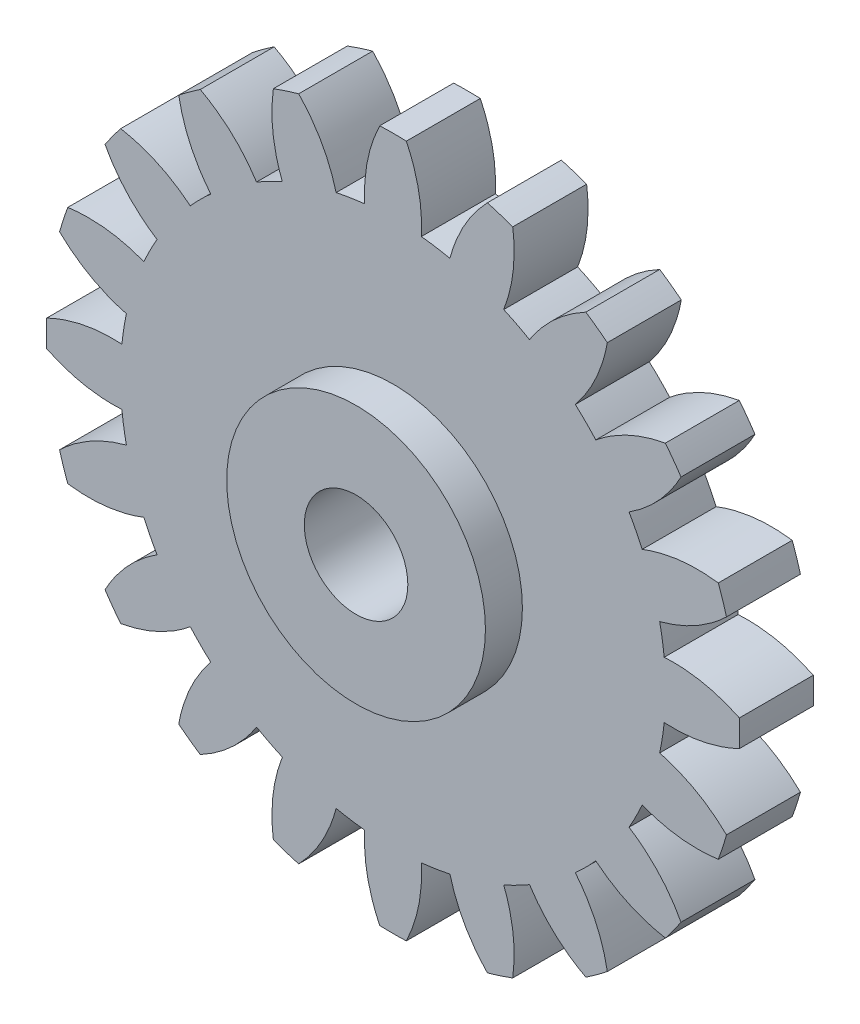
SolidWorks part; units mm, degrees
ref_plane "Front" through (0, 0, 0) normal (0, 0, 1) x (1, 0, 0)
ref_plane "Top" through (0, 0, 0) normal (0, 1, 0) x (1, 0, 0)
ref_plane "Right" through (0, 0, 0) normal (1, 0, 0) x (0, 0, -1)
sketch "草图1" plane through (0, 0, 0) normal (0, 0, 1) x (1, 0, 0)
  line L0 (0, 5.5081) -> (0, -0.6703) construction
  line L1 (0, 0) -> (-0.6106, 5.8096) construction
  line L2 (0, 0) -> (0.5998, 5.7068) construction
  arc A0 (-0.3826, 3.6676) -> (-0.7695, 3.6063) centre (0, 0) ccw
  arc A1 (0.18, 4.684) -> (-0.18, 4.684) centre (0, 0) ccw
  arc A3 (1.6186, 4.3992) -> (1.2763, 4.5104) centre (0, 0) ccw
  arc A4 (2.8988, 3.6837) -> (2.6076, 3.8953) centre (0, 0) ccw
  arc A5 (3.8953, 2.6076) -> (3.6837, 2.8988) centre (0, 0) ccw
  arc A6 (4.5104, 1.2763) -> (4.3992, 1.6186) centre (0, 0) ccw
  arc A7 (4.684, -0.18) -> (4.684, 0.18) centre (0, 0) ccw
  arc A8 (4.3992, -1.6186) -> (4.5104, -1.2763) centre (0, 0) ccw
  arc A9 (3.6837, -2.8988) -> (3.8953, -2.6076) centre (0, 0) ccw
  arc A10 (2.6076, -3.8953) -> (2.8988, -3.6837) centre (0, 0) ccw
  arc A11 (1.2763, -4.5104) -> (1.6186, -4.3992) centre (0, 0) ccw
  arc A12 (-0.18, -4.684) -> (0.18, -4.684) centre (0, 0) ccw
  arc A13 (-1.6186, -4.3992) -> (-1.2763, -4.5104) centre (0, 0) ccw
  arc A14 (-2.8988, -3.6837) -> (-2.6076, -3.8953) centre (0, 0) ccw
  arc A15 (-3.8953, -2.6076) -> (-3.6837, -2.8988) centre (0, 0) ccw
  arc A16 (-4.5104, -1.2763) -> (-4.3992, -1.6186) centre (0, 0) ccw
  arc A17 (-4.684, 0.18) -> (-4.684, -0.18) centre (0, 0) ccw
  arc A18 (-4.3992, 1.6186) -> (-4.5104, 1.2763) centre (0, 0) ccw
  arc A19 (-3.6837, 2.8988) -> (-3.8953, 2.6076) centre (0, 0) ccw
  arc A20 (-2.6076, 3.8953) -> (-2.8988, 3.6837) centre (0, 0) ccw
  arc A21 (-1.2763, 4.5104) -> (-1.6186, 4.3992) centre (0, 0) ccw
  arc A22 (0.7695, 3.6063) -> (0.3826, 3.6676) centre (0, 0) ccw
  arc A23 (1.8462, 3.192) -> (1.4972, 3.3699) centre (0, 0) ccw
  arc A24 (2.7422, 2.4653) -> (2.4653, 2.7422) centre (0, 0) ccw
  arc A25 (3.3699, 1.4972) -> (3.192, 1.8462) centre (0, 0) ccw
  arc A26 (3.6676, 0.3826) -> (3.6063, 0.7695) centre (0, 0) ccw
  arc A27 (3.6063, -0.7695) -> (3.6676, -0.3826) centre (0, 0) ccw
  arc A28 (3.192, -1.8462) -> (3.3699, -1.4972) centre (0, 0) ccw
  arc A29 (2.4653, -2.7422) -> (2.7422, -2.4653) centre (0, 0) ccw
  arc A30 (1.4972, -3.3699) -> (1.8462, -3.192) centre (0, 0) ccw
  arc A31 (-1.4972, 3.3699) -> (-1.8462, 3.192) centre (0, 0) ccw
  arc A32 (-2.4653, 2.7422) -> (-2.7422, 2.4653) centre (0, 0) ccw
  arc A33 (-3.192, 1.8462) -> (-3.3699, 1.4972) centre (0, 0) ccw
  arc A34 (-3.6063, 0.7695) -> (-3.6676, 0.3826) centre (0, 0) ccw
  arc A35 (-3.6676, -0.3826) -> (-3.6063, -0.7695) centre (0, 0) ccw
  arc A36 (-3.3699, -1.4972) -> (-3.192, -1.8462) centre (0, 0) ccw
  arc A37 (-2.7422, -2.4653) -> (-2.4653, -2.7422) centre (0, 0) ccw
  arc A38 (-1.8462, -3.192) -> (-1.4972, -3.3699) centre (0, 0) ccw
  arc A39 (-0.7695, -3.6063) -> (-0.3826, -3.6676) centre (0, 0) ccw
  arc A40 (0.3826, -3.6676) -> (0.7695, -3.6063) centre (0, 0) ccw
  spline S0 degree 2 poles (0.18, 4.684) (0.4125, 4.2014) (0.3826, 3.6676) knots 0 0 0 1 1 1
  spline S1 degree 2 poles (-0.18, 4.684) (-0.4125, 4.2014) (-0.3826, 3.6676) knots 0 0 0 1 1 1
  spline S2 degree 2 poles (1.2763, 4.5104) (0.906, 4.1233) (0.7695, 3.6063) knots 0 0 0 1 1 1
  spline S3 degree 2 poles (1.6186, 4.3992) (1.6907, 3.8683) (1.4972, 3.3699) knots 0 0 0 1 1 1
  spline S4 degree 2 poles (2.6076, 3.8953) (2.1358, 3.6415) (1.8462, 3.192) knots 0 0 0 1 1 1
  spline S5 degree 2 poles (2.8988, 3.6837) (2.8033, 3.1566) (2.4653, 2.7422) knots 0 0 0 1 1 1
  spline S6 degree 2 poles (3.6837, 2.8988) (3.1566, 2.8033) (2.7422, 2.4653) knots 0 0 0 1 1 1
  spline S7 degree 2 poles (3.8953, 2.6076) (3.6415, 2.1358) (3.192, 1.8462) knots 0 0 0 1 1 1
  spline S8 degree 2 poles (4.3992, 1.6186) (3.8683, 1.6907) (3.3699, 1.4972) knots 0 0 0 1 1 1
  spline S9 degree 2 poles (4.5104, 1.2763) (4.1233, 0.906) (3.6063, 0.7695) knots 0 0 0 1 1 1
  spline S10 degree 2 poles (4.684, 0.18) (4.2014, 0.4125) (3.6676, 0.3826) knots 0 0 0 1 1 1
  spline S11 degree 2 poles (4.684, -0.18) (4.2014, -0.4125) (3.6676, -0.3826) knots 0 0 0 1 1 1
  spline S12 degree 2 poles (4.5104, -1.2763) (4.1233, -0.906) (3.6063, -0.7695) knots 0 0 0 1 1 1
  spline S13 degree 2 poles (4.3992, -1.6186) (3.8683, -1.6907) (3.3699, -1.4972) knots 0 0 0 1 1 1
  spline S14 degree 2 poles (3.8953, -2.6076) (3.6415, -2.1358) (3.192, -1.8462) knots 0 0 0 1 1 1
  spline S15 degree 2 poles (3.6837, -2.8988) (3.1566, -2.8033) (2.7422, -2.4653) knots 0 0 0 1 1 1
  spline S16 degree 2 poles (2.8988, -3.6837) (2.8033, -3.1566) (2.4653, -2.7422) knots 0 0 0 1 1 1
  spline S17 degree 2 poles (2.6076, -3.8953) (2.1358, -3.6415) (1.8462, -3.192) knots 0 0 0 1 1 1
  spline S18 degree 2 poles (1.6186, -4.3992) (1.6907, -3.8683) (1.4972, -3.3699) knots 0 0 0 1 1 1
  spline S19 degree 2 poles (1.2763, -4.5104) (0.906, -4.1233) (0.7695, -3.6063) knots 0 0 0 1 1 1
  spline S20 degree 2 poles (0.18, -4.684) (0.4125, -4.2014) (0.3826, -3.6676) knots 0 0 0 1 1 1
  spline S21 degree 2 poles (-0.18, -4.684) (-0.4125, -4.2014) (-0.3826, -3.6676) knots 0 0 0 1 1 1
  spline S22 degree 2 poles (-1.2763, -4.5104) (-0.906, -4.1233) (-0.7695, -3.6063) knots 0 0 0 1 1 1
  spline S23 degree 2 poles (-1.6186, -4.3992) (-1.6907, -3.8683) (-1.4972, -3.3699) knots 0 0 0 1 1 1
  spline S24 degree 2 poles (-2.6076, -3.8953) (-2.1358, -3.6415) (-1.8462, -3.192) knots 0 0 0 1 1 1
  spline S25 degree 2 poles (-2.8988, -3.6837) (-2.8033, -3.1566) (-2.4653, -2.7422) knots 0 0 0 1 1 1
  spline S26 degree 2 poles (-3.6837, -2.8988) (-3.1566, -2.8033) (-2.7422, -2.4653) knots 0 0 0 1 1 1
  spline S27 degree 2 poles (-3.8953, -2.6076) (-3.6415, -2.1358) (-3.192, -1.8462) knots 0 0 0 1 1 1
  spline S28 degree 2 poles (-4.3992, -1.6186) (-3.8683, -1.6907) (-3.3699, -1.4972) knots 0 0 0 1 1 1
  spline S29 degree 2 poles (-4.5104, -1.2763) (-4.1233, -0.906) (-3.6063, -0.7695) knots 0 0 0 1 1 1
  spline S30 degree 2 poles (-4.684, -0.18) (-4.2014, -0.4125) (-3.6676, -0.3826) knots 0 0 0 1 1 1
  spline S31 degree 2 poles (-4.684, 0.18) (-4.2014, 0.4125) (-3.6676, 0.3826) knots 0 0 0 1 1 1
  spline S32 degree 2 poles (-4.5104, 1.2763) (-4.1233, 0.906) (-3.6063, 0.7695) knots 0 0 0 1 1 1
  spline S33 degree 2 poles (-4.3992, 1.6186) (-3.8683, 1.6907) (-3.3699, 1.4972) knots 0 0 0 1 1 1
  spline S34 degree 2 poles (-3.8953, 2.6076) (-3.6415, 2.1358) (-3.192, 1.8462) knots 0 0 0 1 1 1
  spline S35 degree 2 poles (-3.6837, 2.8988) (-3.1566, 2.8033) (-2.7422, 2.4653) knots 0 0 0 1 1 1
  spline S36 degree 2 poles (-2.8988, 3.6837) (-2.8033, 3.1566) (-2.4653, 2.7422) knots 0 0 0 1 1 1
  spline S37 degree 2 poles (-2.6076, 3.8953) (-2.1358, 3.6415) (-1.8462, 3.192) knots 0 0 0 1 1 1
  spline S38 degree 2 poles (-1.6186, 4.3992) (-1.6907, 3.8683) (-1.4972, 3.3699) knots 0 0 0 1 1 1
  spline S39 degree 2 poles (-1.2763, 4.5104) (-0.906, 4.1233) (-0.7695, 3.6063) knots 0 0 0 1 1 1
  point P7 (0, 4.6875)
  point P10 (0, 4.1875)
  point P11 (-0.18, 4.684)
  point P12 (0.18, 4.684)
  point P13 (-0.35, 4.1728)
  point P14 (0.35, 4.1728)
  point P15 (0, 3.6875)
  point P16 (-0.3826, 3.6676)
  point P17 (0.3826, 3.6676)
  point P137 (0, 0)
  dimension "D1" = 7.375
  dimension "D2" = 0.18
  dimension "D3" = 20
  dimension "D4" = 9.375
  dimension "D5" = 0.18
  dimension "D6" = 0.35
  dimension "D7" = 0.35
extrude "凸台-拉伸1" add sketch "草图1" along normal mid plane 1
sketch "草图2" plane through (0, 0, -0.5) normal (0, 0, -1) x (-1, 0, 0)
  circle A0 centre (0, 0) radius 1.75
  dimension "D1" = 3.5
extrude "凸台-拉伸2" add sketch "草图2" along normal blind 0.5
sketch "草图3" plane through (0, 0, 0.5) normal (0, 0, 1) x (1, 0, 0)
  circle A0 centre (0, 0) radius 1.75
  dimension "D1" = 3.5
extrude "凸台-拉伸3" add sketch "草图3" along normal blind 0.5
sketch "草图4" plane through (0, 0, 0) normal (0, 0, 1) x (1, 0, 0)
  circle A0 centre (0, 0) radius 0.7
  dimension "D1" = 1.4
extrude "切除-拉伸1" cut sketch "草图4" against normal through all both and the other way through all
